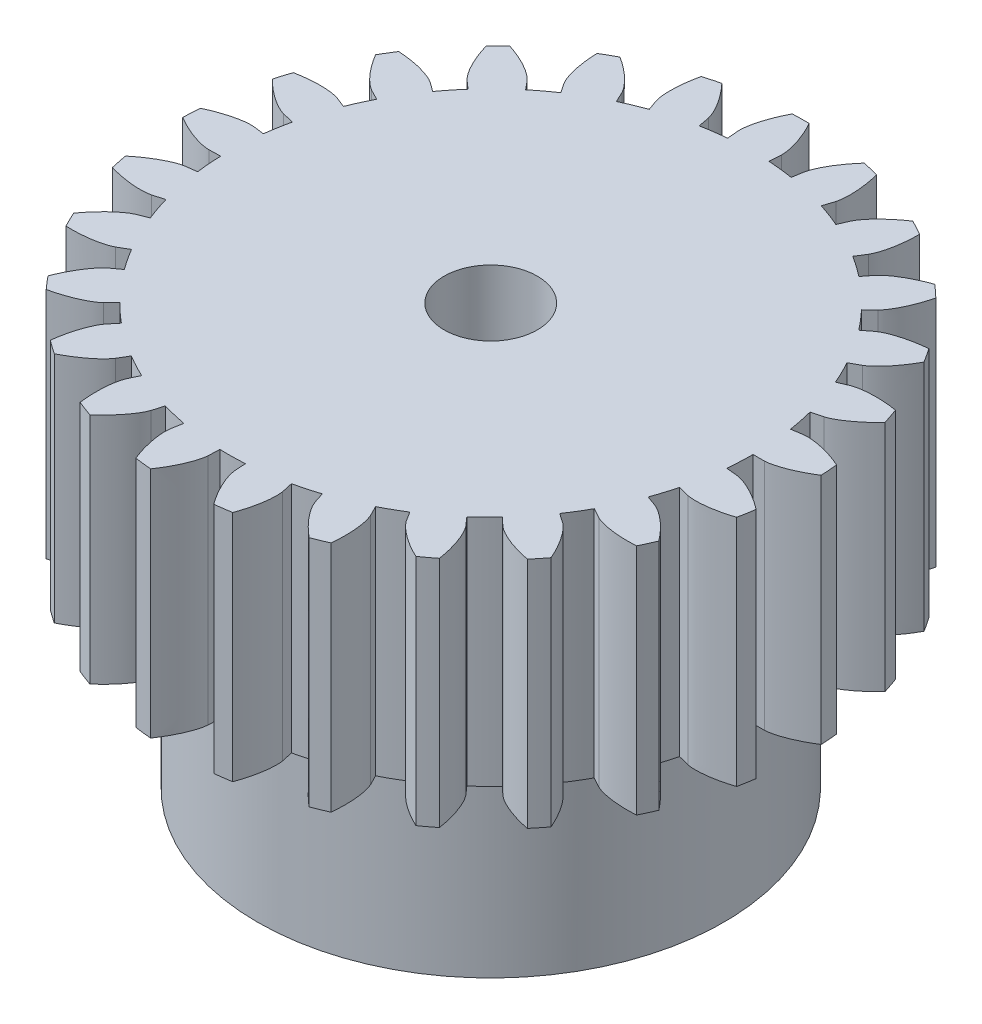
SolidWorks part; units mm, degrees
ref_plane "前视基准面" through (0, 0, 0) normal (0, 0, 1) x (1, 0, 0)
ref_plane "上视基准面" through (0, 0, 0) normal (0, 1, 0) x (1, 0, 0)
ref_plane "右视基准面" through (0, 0, 0) normal (1, 0, 0) x (0, 0, -1)
sketch "草图2" plane through (0, 0, 0) normal (0, 1, 0) x (1, 0, 0)
  line L0 (0, 0) -> (13.4592, 1.0485) construction
  line L1 (11.7462, 0) -> (11.25, 0)
  line L2 (11.6044, 1.8191) -> (11.1143, 1.7422)
  circle A0 centre (0, 0) radius 11.7462
  circle A3 centre (0, 0) radius 11.25
  circle A4 centre (0, 0) radius 12.5
  circle A5 centre (0, 0) radius 13.5
  spline S0 degree 4 poles (11.7462, 0) (11.7908, 0.0022) (11.8797, 0.0109) (12.0471, 0.0423) (12.289, 0.108) (12.6971, 0.2542) (13.3156, 0.5585) (14.0871, 1.0763) (15.0502, 1.9469) (16.0137, 3.1244) (16.8754, 4.5566) (17.582, 6.2129) (18.0781, 7.9429) (18.3756, 9.7173) (18.4915, 11.6014) (18.391, 13.9368) (17.9148, 16.6878) (16.9006, 19.7704) (15.2584, 22.9792) (13.1729, 25.9172) (10.7109, 28.5458) (8.2815, 30.5517) (6.0386, 32.0496) (4.0793, 33.147) (2.4638, 33.9334) (0.8071, 34.6277) (-0.886, 35.2297) (-3.0385, 35.8666) (-5.2346, 36.3501) (-7.2316, 36.6483) (-8.9127, 36.7983) (-9.8025, 36.8524) (-10.4099, 36.8783) (-10.8851, 36.8939) (-11.5589, 36.903) (-12.0614, 36.9021) (-12.8882, 36.8886) (-13.5235, 36.8603) (-14.301, 36.8181) (-14.9896, 36.7619) (-15.7332, 36.6919) (-16.436, 36.6083) (-16.9876, 36.5354) (-17.3381, 36.4823) (-17.5203, 36.4546) knots 0 0 0 0 0 0.002802 0.005604 0.010661 0.015718 0.02996 0.048734 0.068727 0.096889 0.125051 0.153212 0.181374 0.209535 0.237696 0.271429 0.327752 0.384075 0.440398 0.496721 0.553044 0.609367 0.637529 0.66569 0.693852 0.722013 0.750174 0.778336 0.834659 0.86282 0.876901 0.883942 0.890982 0.900036 0.909091 0.920455 0.931818 0.943182 0.954545 0.965909 0.977273 0.988636 1 1 1 1 1 construction
  spline S1 degree 4 poles (11.7462, 0) (11.7908, 0.0022) (11.8797, 0.0109) (12.0471, 0.0423) (12.289, 0.108) (12.6971, 0.2542) (13.3156, 0.5585) (14.0871, 1.0763) (15.0502, 1.9469) (16.0137, 3.1244) (16.8754, 4.5566) (17.582, 6.2129) (18.0781, 7.9429) (18.3756, 9.7173) (18.4915, 11.6014) (18.391, 13.9368) (17.9148, 16.6878) (16.9006, 19.7704) (15.2584, 22.9792) (13.1729, 25.9172) (10.7109, 28.5458) (8.2815, 30.5517) (6.0386, 32.0496) (4.0793, 33.147) (2.4638, 33.9334) (0.8071, 34.6277) (-0.886, 35.2297) (-3.0385, 35.8666) (-5.2346, 36.3501) (-7.2316, 36.6483) (-8.9127, 36.7983) (-9.8025, 36.8524) (-10.4099, 36.8783) (-10.8851, 36.8939) (-11.3492, 36.9001) (-11.6149, 36.9016) (-11.7462, 36.9016) knots 0 0 0 0 0 0.002802 0.005604 0.010661 0.015718 0.02996 0.048734 0.068727 0.096889 0.125051 0.153212 0.181374 0.209535 0.237696 0.271429 0.327752 0.384075 0.440398 0.496721 0.553044 0.609367 0.637529 0.66569 0.693852 0.722013 0.750174 0.778336 0.834659 0.86282 0.876901 0.883942 0.890982 0.900036 0.909091 0.909091 0.909091 0.909091 0.909091
  spline S2 degree 4 poles (11.6044, 1.8191) (11.6489, 1.8238) (11.7381, 1.829) (11.9083, 1.8239) (12.1575, 1.7964) (12.5833, 1.7153) (13.2414, 1.5104) (14.0838, 1.1183) (15.1701, 0.4074) (16.3044, -0.6067) (17.3775, -1.8882) (18.332, -3.4151) (19.0901, -5.0474) (19.6588, -6.7543) (20.0651, -8.5977) (20.3275, -10.9206) (20.283, -13.7121) (19.7584, -16.9146) (18.633, -20.339) (17.0277, -23.5645) (15.0024, -26.5427) (12.913, -28.9006) (10.9291, -30.7278) (9.1634, -32.1154) (7.6892, -33.1425) (6.16, -34.085) (4.5805, -34.9419) (2.5527, -35.9045) (0.458, -36.7222) (-1.4688, -37.326) (-3.1064, -37.7346) (-3.9771, -37.9258) (-4.5732, -38.0456) (-5.0402, -38.1345) (-5.4977, -38.2126) (-5.76, -38.2552) (-5.8897, -38.2755) knots 0 0 0 0 0 0.002802 0.005604 0.010661 0.015718 0.02996 0.048734 0.068727 0.096889 0.125051 0.153212 0.181374 0.209535 0.237696 0.271429 0.327752 0.384075 0.440398 0.496721 0.553044 0.609367 0.637529 0.66569 0.693852 0.722013 0.750174 0.778336 0.834659 0.86282 0.876901 0.883942 0.890982 0.900036 0.909091 0.909091 0.909091 0.909091 0.909091
  point P6 (13.4284, 1.3888)
  point P12 (12.4023, 1.5598)
  point P14 (12.4986, 0.1863)
  point P15 (13.4824, 0.6892)
  point P19 (12.4622, 0.9708)
  dimension "D1" = 22.5
  dimension "D2" = 23.4923
  dimension "D3" = 25
  dimension "D4" = 27
  dimension "D6" = 0.7854
extrude "凸台-拉伸1" add sketch "草图2" along normal blind 10
pattern_circular "阵列(圆周)1" count 25 every 14.4 about axis through (0, 10, 0) along (0, -1, 0) of "凸台-拉伸1"
sketch "草图3" plane through (0, 0, 0) normal (0, -1, 0) x (-1, 0, 0)
  circle A0 centre (0, 0) radius 2
  dimension "D1" = 4
extrude "切除-拉伸1" cut sketch "草图3" against normal through all
sketch "草图4" plane through (0, 0, 0) normal (0, -1, 0) x (-1, 0, 0)
  circle A0 centre (0, 0) radius 10
  circle A1 centre (0, 0) radius 2
  dimension "D1" = 20
  dimension "D2" = 4
extrude "凸台-拉伸2" add sketch "草图4" along normal blind 8
equation "\"m\"= 1'齿轮模数"
equation "\"z\"= 25'齿轮齿数"
equation "\"D\"= \"m\" * \"z\"'分度圆直径"
equation "\"Db\"= \"D\" * cos ( 20 )'基圆直径"
equation "\"Df\"= ( \"z\" - 2.5 ) * \"m\"'齿根圆直径"
equation "\"Da\"= ( \"z\" + 2 ) * \"m\"'齿顶圆直径"
equation "\"D1@草图2\"= \"Df\"'齿根圆"
equation "\"D2@草图2\"= \"Db\"'基圆"
equation "\"s\"= \"m\" * pi / 2'齿厚"
equation "\"D3@草图2\"= \"D\"'分度圆"
equation "\"D4@草图2\"= \"Da\"'齿顶圆"
equation "\"D6@草图2\"= \"s\" * 0.5"
